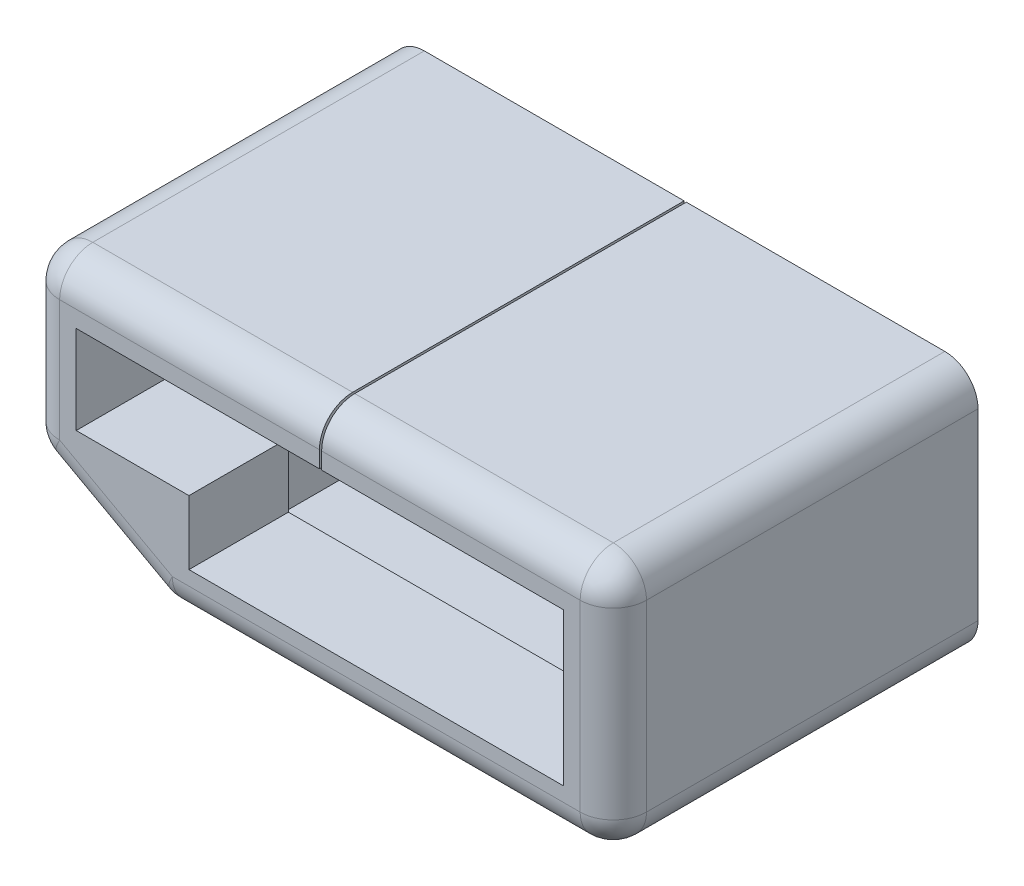
SolidWorks part; units mm, degrees
ref_plane "Alzado" through (0, 0, 0) normal (0, 0, 1) x (1, 0, 0)
ref_plane "Planta" through (0, 0, 0) normal (0, 1, 0) x (1, 0, 0)
ref_plane "Vista lateral" through (0, 0, 0) normal (1, 0, 0) x (0, 0, -1)
sketch "Croquis1" plane through (0, 0, 0) normal (0, 0, 1) x (1, 0, 0)
  line L5 (-6.7038, -4.1399) -> (11.7462, -4.1399)
  line L7 (-11.8038, 4.1601) -> (-0.05, 4.1601)
  line L8 (11.7462, -4.1399) -> (11.7462, 4.1601)
  line L9 (-11.8038, -4.1805) -> (11.7462, 4.1601) construction
  line L10 (-11.8038, 4.1601) -> (11.7462, -4.1399) construction
  line L11 (-11.8038, 5.6601) -> (-0.05, 5.6601)
  line L12 (13.2462, 4.1601) -> (13.2462, -4.1399)
  line L13 (11.7462, -5.6399) -> (-11.8038, -5.6399)
  line L15 (-6.7038, -1.3399) -> (-6.7038, -4.1399)
  line L16 (-6.7038, -1.3399) -> (-11.8038, -1.3399)
  line L17 (-13.3038, 4.1601) -> (-13.3038, -4.1399)
  line L18 (-11.8038, -1.3399) -> (-11.8038, 4.1601)
  line L20 (0, 0) -> (0, 8.2706) construction
  line L21 (-0.05, 5.6601) -> (-0.05, 4.1601)
  line L22 (0.05, 5.6601) -> (0.05, 4.1601)
  line L23 (0.05, 4.1601) -> (11.7462, 4.1601)
  line L24 (0.05, 5.6601) -> (11.7462, 5.6601)
  arc A0 (11.7462, 5.6601) -> (13.2462, 4.1601) centre (11.7462, 4.1601) cw
  arc A1 (13.2462, -4.1399) -> (11.7462, -5.6399) centre (11.7462, -4.1399) cw
  arc A2 (-11.8038, 5.6601) -> (-13.3038, 4.1601) centre (-11.8038, 4.1601) ccw
  arc A3 (-13.3038, -4.1399) -> (-11.8038, -5.6399) centre (-11.8038, -4.1399) ccw
  point P0 (0, 0)
  dimension "D9" = 1.5
  dimension "D1" = 23.55
  dimension "D2" = 8.3
  dimension "D3" = 5.5
  dimension "D4" = 18.45
  dimension "D5" = 1.5
  dimension "D6" = 1.5
  dimension "D7" = 1.5
  dimension "D8" = 0.05
extrude "Saliente-Extruir1" add sketch "Croquis1" along normal blind 12
sketch "Croquis2" plane through (0, 0, 12) normal (0, 0, 1) x (1, 0, 0)
  line L0 (-11.8038, -5.6399) -> (11.7462, -5.6399) construction
  line L1 (13.2462, -4.1399) -> (13.2462, 4.1601) construction
  line L3 (-11.8038, -5.6399) -> (11.7462, -5.6399)
  line L4 (13.2462, -4.1399) -> (13.2462, 4.1601)
  line L5 (11.7462, 5.6601) -> (0.05, 5.6601)
  line L6 (-10.7451, 3.4101) -> (-11.0538, 3.4101)
  line L7 (-5.9538, -3.4899) -> (10.9962, -3.4899)
  line L9 (-10.7451, 3.4101) -> (-0.05, 3.4101)
  line L10 (10.9962, -3.4899) -> (10.9962, 3.4101)
  line L11 (-5.9538, -1.8464) -> (10.9962, 3.4101) construction
  line L12 (-10.7451, 3.4101) -> (10.9962, -3.4899) construction
  line L14 (-11.0538, -0.5899) -> (-5.9538, -0.5899)
  line L15 (-5.9538, -0.5899) -> (-5.9538, -3.4899)
  line L17 (-11.8038, 4.1601) -> (-0.05, 4.1601) construction
  line L18 (11.7462, 4.1601) -> (11.7462, -4.1399) construction
  line L19 (-6.7038, -4.1399) -> (-6.7038, -1.3399) construction
  line L20 (-6.7038, -1.3399) -> (-11.8038, -1.3399) construction
  line L23 (-0.05, 5.6601) -> (-11.8038, 5.6601) construction
  line L24 (-13.3038, 4.1601) -> (-13.3038, -4.1399) construction
  line L25 (-13.3038, 4.1601) -> (-13.3038, -4.1399)
  line L26 (-11.0538, -0.5899) -> (-11.0538, 3.4101)
  line L27 (-11.8038, -1.3399) -> (-11.8038, 4.1601) construction
  line L28 (-0.05, 3.4101) -> (-0.05, 5.6601)
  line L29 (0.05, 3.4101) -> (0.05, 5.6601)
  line L30 (0.05, 3.4101) -> (10.9962, 3.4101)
  line L31 (-0.05, 5.6601) -> (-11.8038, 5.6601)
  arc A0 (11.7462, -5.6399) -> (13.2462, -4.1399) centre (11.7462, -4.1399) ccw construction
  arc A1 (13.2462, 4.1601) -> (11.7462, 5.6601) centre (11.7462, 4.1601) ccw construction
  arc A2 (11.7462, -5.6399) -> (13.2462, -4.1399) centre (11.7462, -4.1399) ccw
  arc A3 (13.2462, 4.1601) -> (11.7462, 5.6601) centre (11.7462, 4.1601) ccw
  arc A4 (-11.8038, 5.6601) -> (-13.3038, 4.1601) centre (-11.8038, 4.1601) ccw construction
  arc A5 (-13.3038, -4.1399) -> (-11.8038, -5.6399) centre (-11.8038, -4.1399) ccw construction
  arc A6 (-11.8038, 5.6601) -> (-13.3038, 4.1601) centre (-11.8038, 4.1601) ccw
  arc A7 (-13.3038, -4.1399) -> (-11.8038, -5.6399) centre (-11.8038, -4.1399) ccw
  point P3 (0, 0)
  dimension "D1" = 6.9
  dimension "D2" = 0.75
  dimension "D3" = 0.75
  dimension "D4" = 0.75
  dimension "D5" = 0.75
  dimension "D6" = 0.75
extrude "Saliente-Extruir2" add sketch "Croquis2" along normal blind 4.5
sketch "Croquis3" plane through (0, 0, 0) normal (0, 0, -1) x (-1, 0, 0)
  line L0 (7.4257, -5.4547) -> (12.5257, -2.6547)
  line L1 (6.7038, -5.6399) -> (6.7038, -7.332)
  line L2 (6.7038, -7.332) -> (14.9858, -7.332)
  line L3 (14.9858, -7.332) -> (14.9858, -1.3399)
  line L4 (14.9858, -1.3399) -> (13.3038, -1.3399)
  line L5 (13.3038, 4.1601) -> (13.3038, -4.1399) construction
  line L6 (11.8038, -5.6399) -> (-11.7462, -5.6399) construction
  arc A0 (6.7038, -5.6399) -> (7.4257, -5.4547) centre (6.7038, -4.1399) ccw
  arc A1 (12.5257, -2.6547) -> (13.3038, -1.3399) centre (11.8038, -1.3399) ccw
extrude "Cortar-Extruir1" cut sketch "Croquis3" against normal blind 17
fillet "Redondeo1" radius 1.5 11 edges at (-5.9269, 5.6601, 16.5) (-12.8644, 5.2208, 16.5) (-13.3038, 1.4101, 16.5) (-13.0947, -2.1038, 16.5) (-9.9757, -4.0547, 16.5) (-7.0764, -5.5928, 16.5) (5.8981, 5.6601, 16.5) (12.8069, 5.2208, 16.5) (13.2462, 0.0101, 16.5) (12.8069, -5.2005, 16.5) (2.5212, -5.6399, 16.5)
